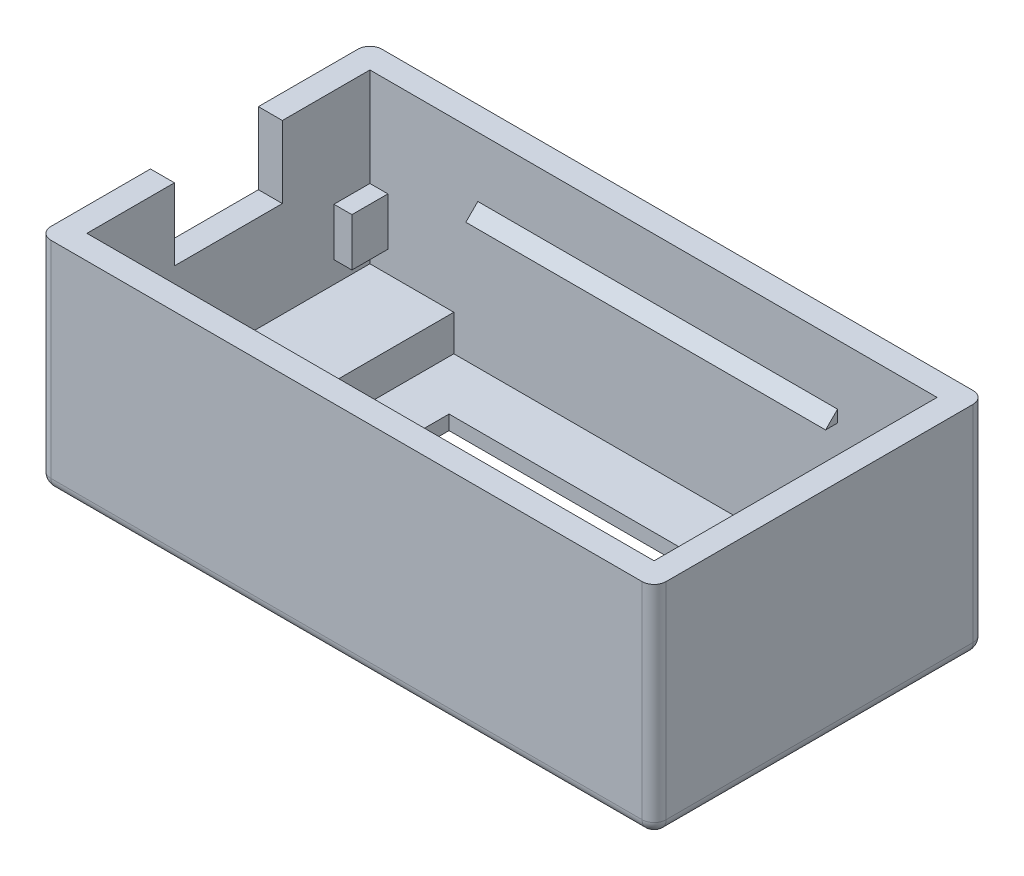
SolidWorks part; units mm, degrees
ref_plane "Front Plane" through (0, 0, 0) normal (0, 0, 1) x (1, 0, 0)
ref_plane "Top Plane" through (0, 0, 0) normal (0, 1, 0) x (1, 0, 0)
ref_plane "Right Plane" through (0, 0, 0) normal (1, 0, 0) x (0, 0, -1)
sketch "Sketch1" plane through (0, 0, 0) normal (0, 1, 0) x (1, 0, 0)
  line L1 (0, 0) -> (47.3, 0)
  line L2 (0, 0) -> (0, 23.6)
  line L3 (0, 23.6) -> (47.3, 23.6)
  line L4 (47.3, 0) -> (47.3, 23.6)
  dimension "D1" = 47.3
  dimension "D2" = 23.6
extrude "Extrude-Thin1" add sketch "Sketch1" along normal blind 17 thin
sketch "Sketch2" plane through (0, 0, 0) normal (0, -1, 0) x (1, 0, 0)
  line L1 (-2, -25.6) -> (49.3, -25.6)
  line L2 (-2, -25.6) -> (-2, 2)
  line L3 (-2, 2) -> (49.3, 2)
  line L4 (49.3, -25.6) -> (49.3, 2)
extrude "Boss-Extrude1" add sketch "Sketch2" along normal blind 1.2
sketch "Sketch3" plane through (0, 0, 0) normal (0, 1, 0) x (1, 0, 0)
  line L0 (0, 11.8) -> (47.3, 11.8) construction
  line L1 (0, 23.6) -> (0, 0) construction
  line L2 (47.3, 0) -> (47.3, 23.6) construction
  line L3 (23.65, 23.6) -> (23.65, 0) construction
  line L4 (41.65, 4.55) -> (11.15, 4.55)
  line L5 (41.65, 4.55) -> (41.65, 19.05)
  line L6 (41.65, 19.05) -> (11.15, 19.05)
  line L7 (11.15, 4.55) -> (11.15, 19.05)
  line L8 (41.65, 4.55) -> (11.15, 19.05) construction
  line L9 (41.65, 19.05) -> (11.15, 4.55) construction
  line L10 (47.3, 23.6) -> (0, 23.6) construction
  line L11 (0, 0) -> (47.3, 0) construction
  point P6 (26.4, 11.8)
  dimension "D1" = 30.5
  dimension "D2" = 14.5
  dimension "D3" = 18
extrude "Cut-Extrude1" cut sketch "Sketch3" against normal blind 10
sketch "Sketch7" plane through (0, 0, 0) normal (0, 1, 0) x (1, 0, 0)
  line L0 (47.3, 23.6) -> (0, 23.6) construction
  line L1 (0, 0) -> (7, 0)
  line L2 (0, 0) -> (0, 23.6)
  line L3 (0, 23.6) -> (7, 23.6)
  line L4 (7, 0) -> (7, 23.6)
  line L5 (0, 0) -> (47.3, 0) construction
  line L6 (47.3, 23.6) -> (41.65, 23.6)
  line L7 (47.3, 23.6) -> (47.3, 0)
  line L8 (47.3, 0) -> (41.65, 0)
  line L9 (41.65, 23.6) -> (41.65, 0)
  line L11 (41.65, 4.55) -> (41.65, 19.05) construction
  dimension "D1" = 7
extrude "Boss-Extrude2" add sketch "Sketch7" along normal blind 3
ref_plane "Plane1" through (24, 0, 0) normal (-1, 0, 0) x (0, 0, 1)
sketch "Sketch9" plane through (24, 0, 0) normal (-1, 0, 0) x (0, 0, 1)
  line L0 (2, 17) -> (-25.6, 17) construction
  line L4 (-23.6, 12) -> (-22.6, 11)
  line L5 (-22.6, 11) -> (-23.6, 11)
  line L6 (-23.6, 17) -> (-23.6, 3) construction
  line L7 (-23.6, 11) -> (-23.6, 12)
  line L8 (-1, 11) -> (0, 11)
  line L9 (0, 12) -> (-1, 11)
  line L10 (0, 11) -> (0, 12)
  point P7 (-23.1, 11)
  dimension "D1" = 1
  dimension "D2" = 1
  dimension "D3" = 6
  dimension "D4" = 6
extrude "Boss-Extrude3" add sketch "Sketch9" along normal blind 15 and the other way blind 15 contours L7 L5 L4
ref_plane "Plane2" through (0, 3, 0) normal (0, 1, 0) x (1, 0, 0)
fillet "Fillet1" radius 1 8 edges at (-2, -1.2, -11.8) (23.65, -1.2, -25.6) (49.3, -1.2, -11.8) (23.65, -1.2, 2) (-2, 7.9, -25.6) (49.3, 7.9, -25.6) (49.3, 7.9, 2) (-2, 7.9, 2)
sketch "Sketch12" plane through (-2, 0, 0) normal (-1, 0, 0) x (0, 0, 1)
  line L0 (-11.8, 17) -> (-11.8, -0.2) construction
  line L1 (-24.6, 17) -> (1, 17) construction
  line L2 (-24.6, -0.2) -> (1, -0.2) construction
  line L4 (-7.3, 11) -> (-16.3, 11)
  line L5 (-7.3, 11) -> (-7.3, 23)
  line L6 (-7.3, 23) -> (-16.3, 23)
  line L7 (-16.3, 11) -> (-16.3, 23)
  line L8 (-7.3, 11) -> (-16.3, 23) construction
  line L9 (-7.3, 23) -> (-16.3, 11) construction
  dimension "D1" = 9
  dimension "D2" = 6
extrude "Cut-Extrude3" cut sketch "Sketch12" against normal blind 10
sketch "Sketch13" plane through (0, 0, 0) normal (0, 1, 0) x (1, 0, 0)
  line L0 (41.65, 23.6) -> (41.65, 0) construction
  line L1 (1.15, 0.55) -> (46.65, 0.55)
  line L2 (1.15, 0.55) -> (1.15, 23.05)
  line L3 (1.15, 23.05) -> (46.65, 23.05)
  line L4 (46.65, 0.55) -> (46.65, 23.05)
  line L5 (41.65, 19.05) -> (11.15, 19.05) construction
  line L6 (11.15, 4.55) -> (41.65, 4.55) construction
  line L7 (11.15, 19.05) -> (11.15, 4.55) construction
  dimension "D1" = 5
  dimension "D2" = 4
  dimension "D3" = 4
  dimension "D4" = 10
ref_plane "Plane5" through (0, 4.8, 0) normal (0, 1, 0) x (1, 0, 0)
sketch "Sketch14" plane through (0, 4.8, 0) normal (0, 1, 0) x (1, 0, 0)
  line L0 (23.65, 25.6) -> (23.65, -2) construction
  line L3 (-2, 11.8) -> (49.3, 11.8) construction
  line L4 (-2, 16.3) -> (-2, 7.3) construction
  line L5 (49.3, -1) -> (49.3, 24.6) construction
  line L7 (0, 23.6) -> (1.5, 23.6)
  line L8 (0, 23.6) -> (0, 20.6)
  line L9 (0, 20.6) -> (1.5, 20.6)
  line L10 (1.5, 23.6) -> (1.5, 20.6)
  line L22 (48.3, 25.6) -> (-1, 25.6) construction
  line L23 (-1, -2) -> (48.3, -2) construction
  line L24 (47.3, 20.6) -> (45.8, 20.6)
  line L25 (45.8, 23.6) -> (45.8, 20.6)
  line L26 (47.3, 23.6) -> (45.8, 23.6)
  line L27 (47.3, 23.6) -> (47.3, 20.6)
  line L28 (47.3, 0) -> (47.3, 3)
  line L29 (47.3, 0) -> (45.8, 0)
  line L30 (45.8, 0) -> (45.8, 3)
  line L31 (47.3, 3) -> (45.8, 3)
  line L32 (0, 3) -> (1.5, 3)
  line L33 (1.5, 0) -> (1.5, 3)
  line L34 (0, 0) -> (1.5, 0)
  line L35 (0, 0) -> (0, 3)
  dimension "D1" = 3
  dimension "D2" = 1.5
extrude "Boss-Extrude4" add sketch "Sketch14" along normal blind 4
